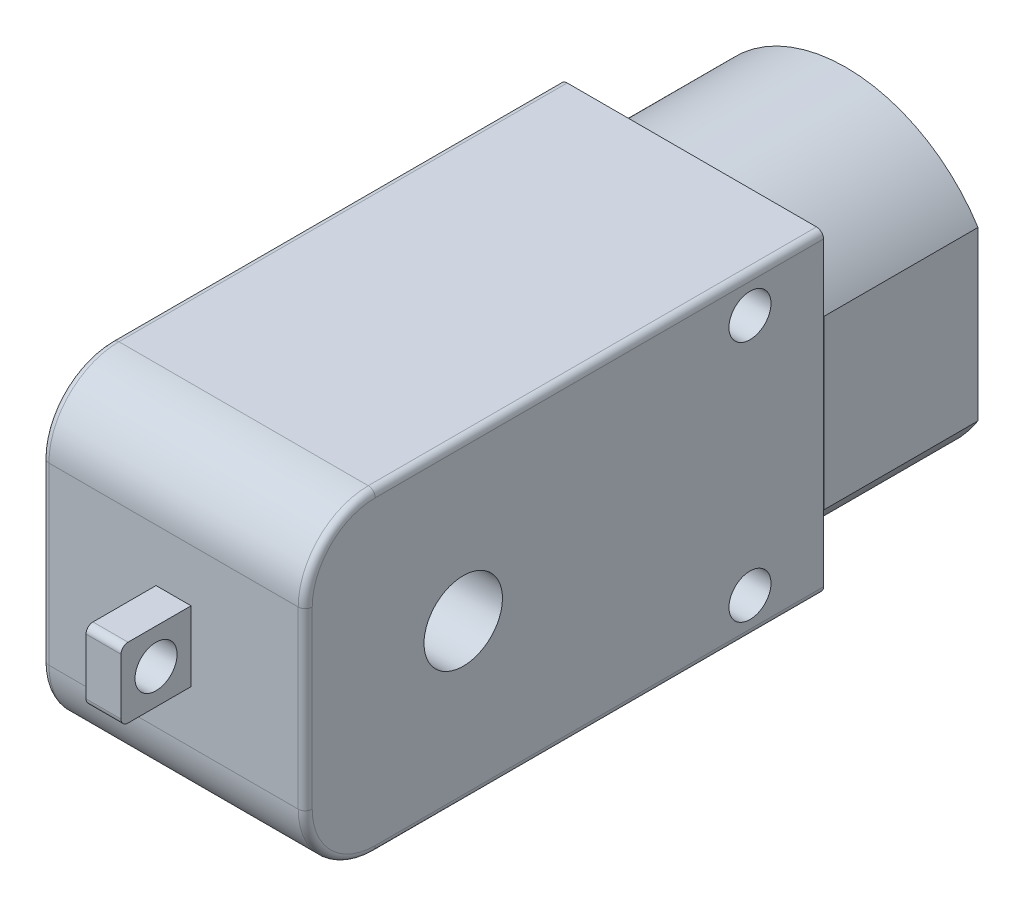
SolidWorks part; units mm, degrees
ref_plane "Front Plane" through (0, 0, 0) normal (0, 0, 1) x (1, 0, 0)
ref_plane "Top Plane" through (0, 0, 0) normal (0, 1, 0) x (1, 0, 0)
ref_plane "Right Plane" through (0, 0, 0) normal (1, 0, 0) x (0, 0, -1)
sketch "Sketch1" plane through (0, 0, 0) normal (0, 0, 1) x (1, 0, 0)
  line L1 (9.4, 11.25) -> (-9.4, 11.25)
  line L2 (9.4, 11.25) -> (9.4, -11.25)
  line L3 (9.4, -11.25) -> (-9.4, -11.25)
  line L4 (-9.4, 11.25) -> (-9.4, -11.25)
  line L5 (9.4, 11.25) -> (-9.4, -11.25) construction
  line L6 (9.4, -11.25) -> (-9.4, 11.25) construction
  point P0 (0, 0)
  dimension "D1" = 22.5
  dimension "D2" = 18.8
extrude "Boss-Extrude1" add sketch "Sketch1" along normal blind 37
sketch "Sketch2" plane through (0, 0, 0) normal (0, 0, -1) x (-1, 0, 0)
  line L0 (9.4, 6.026) -> (9.4, -6.026)
  line L1 (9.4, 11.25) -> (9.4, -11.25) construction
  line L2 (-9.4288, 5.9808) -> (-9.4288, -5.9808)
  arc A0 (9.4, 6.026) -> (-9.4288, 5.9808) centre (0, 0) ccw
  arc A1 (-9.4288, -5.9808) -> (9.4, -6.026) centre (0, 0) ccw
extrude "Boss-Extrude2" add sketch "Sketch2" along normal blind 11
fillet "Fillet1" radius 5 2 edges at (0, -11.25, 37) (0, 11.25, 37)
sketch "Sketch3" plane through (9.4, 0, 0) normal (1, 0, 0) x (0, 0, -1)
  line L0 (-37, -6.25) -> (-37, 6.25) construction
  circle A0 centre (-5.25, 8.65) radius 1.5
  circle A1 centre (-5.25, -8.65) radius 1.5
  dimension "D1" = 17.3
  dimension "D3" = 3
  dimension "D2" = 8.65
  dimension "D4" = 31.75
  dimension "D5" = 0
extrude "Cut-Extrude1" cut sketch "Sketch3" against normal through all
sketch "Sketch4" plane through (0, 0, 37) normal (0, 0, 1) x (1, 0, 0)
  line L1 (1.25, 2.5) -> (-1.25, 2.5)
  line L2 (1.25, 2.5) -> (1.25, -2.5)
  line L3 (1.25, -2.5) -> (-1.25, -2.5)
  line L4 (-1.25, 2.5) -> (-1.25, -2.5)
  line L5 (1.25, 2.5) -> (-1.25, -2.5) construction
  line L6 (1.25, -2.5) -> (-1.25, 2.5) construction
  point P0 (0, 0)
  dimension "D1" = 2.5
  dimension "D2" = 5
extrude "Boss-Extrude3" add sketch "Sketch4" along normal blind 5
fillet "Fillet2" radius 0.5 12 edges at (0, -2.5, 42) (0, 2.5, 42) (-9.4, -11.25, 16) (-9.4, -9.7855, 35.5355) (-9.4, 0, 37) (-9.4, 9.7855, 35.5355) (9.4, -11.25, 16) (9.4, -9.7855, 35.5355) (9.4, 0, 37) (9.4, 9.7855, 35.5355) (-9.4, 11.25, 16) (9.4, 11.25, 16)
sketch "Sketch5" plane through (1.25, 0, 0) normal (1, 0, 0) x (0, 0, -1)
  line L0 (-41.5, 2.5) -> (-37, 2.5) construction
  line L1 (-42, -2) -> (-42, 2) construction
  circle A0 centre (-39.5, 0) radius 1.5
  dimension "D1" = 3
  dimension "D2" = 2.5
  dimension "D3" = 2.5
extrude "Cut-Extrude2" cut sketch "Sketch5" against normal blind 5
sketch "Sketch6" plane through (9.4, 0, 0) normal (1, 0, 0) x (0, 0, -1)
  line L1 (-37, -6.25) -> (-37, 6.25) construction
  circle A0 centre (-25.72, 0) radius 2.8
  dimension "D1" = 5.6
  dimension "D2" = 11.28
extrude "Cut-Extrude3" cut sketch "Sketch6" against normal through all
sketch "Sketch7" plane through (0, 0, -11) normal (0, 0, -1) x (-1, 0, 0)
  line L4 (-8.2288, 5.6215) -> (-8.2288, -5.6215)
  line L5 (8.2, -5.6635) -> (8.2, 5.6635)
  line L6 (-8.2288, 5.6215) -> (-8.2288, -5.6215)
  line L7 (8.2, -5.6635) -> (8.2, 5.6635)
  arc A4 (8.2, 5.6635) -> (-8.2288, 5.6215) centre (0, 0) ccw
  arc A5 (-8.2288, -5.6215) -> (8.2, -5.6635) centre (0, 0) ccw
  arc A6 (8.2, 5.6635) -> (-8.2288, 5.6215) centre (0, 0) ccw
  arc A7 (-8.2288, -5.6215) -> (8.2, -5.6635) centre (0, 0) ccw
  dimension "D1" = 1.2
extrude "Cut-Extrude4" cut sketch "Sketch7" against normal blind 11
sketch "Sketch8" plane through (0, 0, 0) normal (0, 0, -1) x (-1, 0, 0)
  circle A0 centre (0, 0) radius 3
  dimension "D1" = 6
extrude "Cut-Extrude5" cut sketch "Sketch8" against normal blind 2
